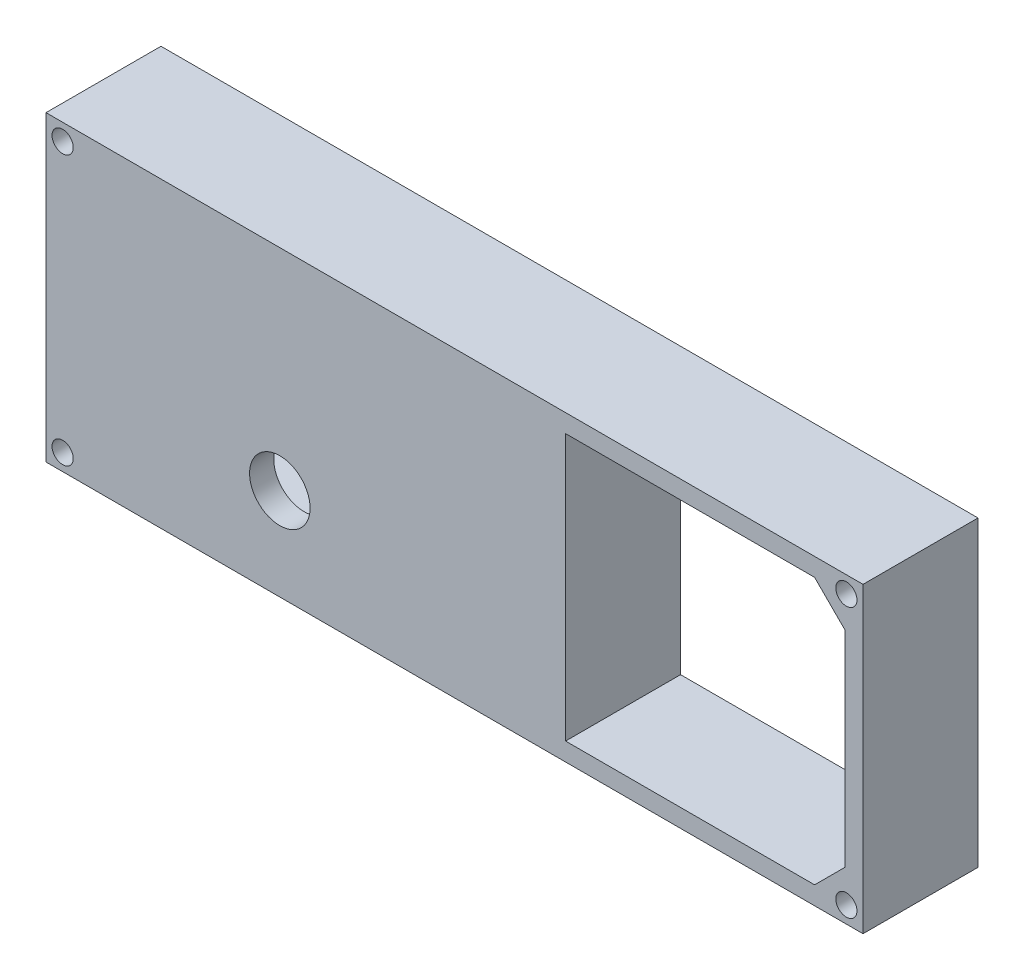
SolidWorks part; units mm, degrees
ref_plane "Alzado" through (0, 0, 0) normal (0, 0, 1) x (1, 0, 0)
ref_plane "Planta" through (0, 0, 0) normal (0, 1, 0) x (1, 0, 0)
ref_plane "Vista lateral" through (0, 0, 0) normal (1, 0, 0) x (0, 0, -1)
sketch "Croquis1" plane through (0, 0, 0) normal (0, 0, 1) x (1, 0, 0)
  line L0 (-67.7624, 25.1114) -> (-67.7624, -24.8886)
  line L1 (-67.7624, -24.8886) -> (67.2376, -24.8886)
  line L2 (67.2376, -24.8886) -> (67.2376, 25.1114)
  line L3 (67.2376, 25.1114) -> (-67.7624, 25.1114)
  line L4 (-64.7624, 17.1114) -> (-64.7624, -16.8886)
  line L5 (-59.7624, 22.1114) -> (-64.7624, 17.1114)
  line L7 (64.2376, 17.1114) -> (59.2376, 22.1114)
  line L8 (64.2376, -16.8886) -> (64.2376, 17.1114)
  line L9 (59.2376, -21.8886) -> (64.2376, -16.8886)
  line L10 (-59.7624, -21.8886) -> (15.0893, -21.8886)
  line L11 (-64.7624, -16.8886) -> (-59.7624, -21.8886)
  line L12 (15.0893, 22.1114) -> (15.0893, -21.8886)
  line L13 (18.0893, 22.1114) -> (18.0893, -21.8886)
  line L14 (59.2376, 22.1114) -> (18.0893, 22.1114)
  line L22 (-59.7624, 22.1114) -> (15.0893, 22.1114)
  line L23 (18.0893, -21.8886) -> (59.2376, -21.8886)
  circle A0 centre (-65.0124, 22.3614) radius 0.85
  circle A1 centre (-65.0124, -22.1386) radius 0.85
  circle A2 centre (64.4876, -22.1386) radius 0.85
  circle A3 centre (64.4876, 22.3614) radius 0.85
extrude "Saliente-Extruir1" add sketch "Croquis1" along normal blind 15
sketch "Croquis2" plane through (0, 0, 15) normal (0, 0, 1) x (1, 0, 0)
  line L0 (18.0893, 22.1114) -> (18.0893, -21.8886)
  line L1 (-67.7624, 25.1114) -> (67.2376, 25.1114)
  line L2 (-67.7624, 25.1114) -> (-67.7624, -24.8886)
  line L3 (-67.7624, -24.8886) -> (67.2376, -24.8886)
  line L4 (67.2376, 25.1114) -> (67.2376, -24.8886)
  line L5 (18.0893, -21.8886) -> (59.2376, -21.8886)
  line L6 (59.2376, -21.8886) -> (64.2376, -16.8886)
  line L7 (64.2376, -16.8886) -> (64.2376, 17.1114)
  line L8 (64.2376, 17.1114) -> (59.2376, 22.1114)
  line L9 (59.2376, 22.1114) -> (18.0893, 22.1114)
  circle A0 centre (-65.0124, 22.3614) radius 0.85
  circle A1 centre (64.4876, 22.3614) radius 0.85
  circle A2 centre (64.4876, -22.1386) radius 0.85
  circle A3 centre (-65.0124, -22.1386) radius 0.85
  circle A4 centre (-29.1269, -9.6674) radius 5
  point P30 (-35.538, -10.8526)
  point P33 (-29.1269, -9.6674)
extrude "Saliente-Extruir2" add sketch "Croquis2" along normal blind 4
sketch "Croquis3" plane through (0, 0, 19) normal (0, 0, 1) x (1, 0, 0)
  circle A0 centre (64.4876, 22.3614) radius 1.75
  circle A1 centre (64.4876, -22.1386) radius 1.75
  circle A2 centre (-65.0124, -22.1386) radius 1.75
  circle A3 centre (-65.0124, 22.3614) radius 1.75
  dimension "D1" = 3.5
extrude "Cortar-Extruir1" cut sketch "Croquis3" against normal blind 12
